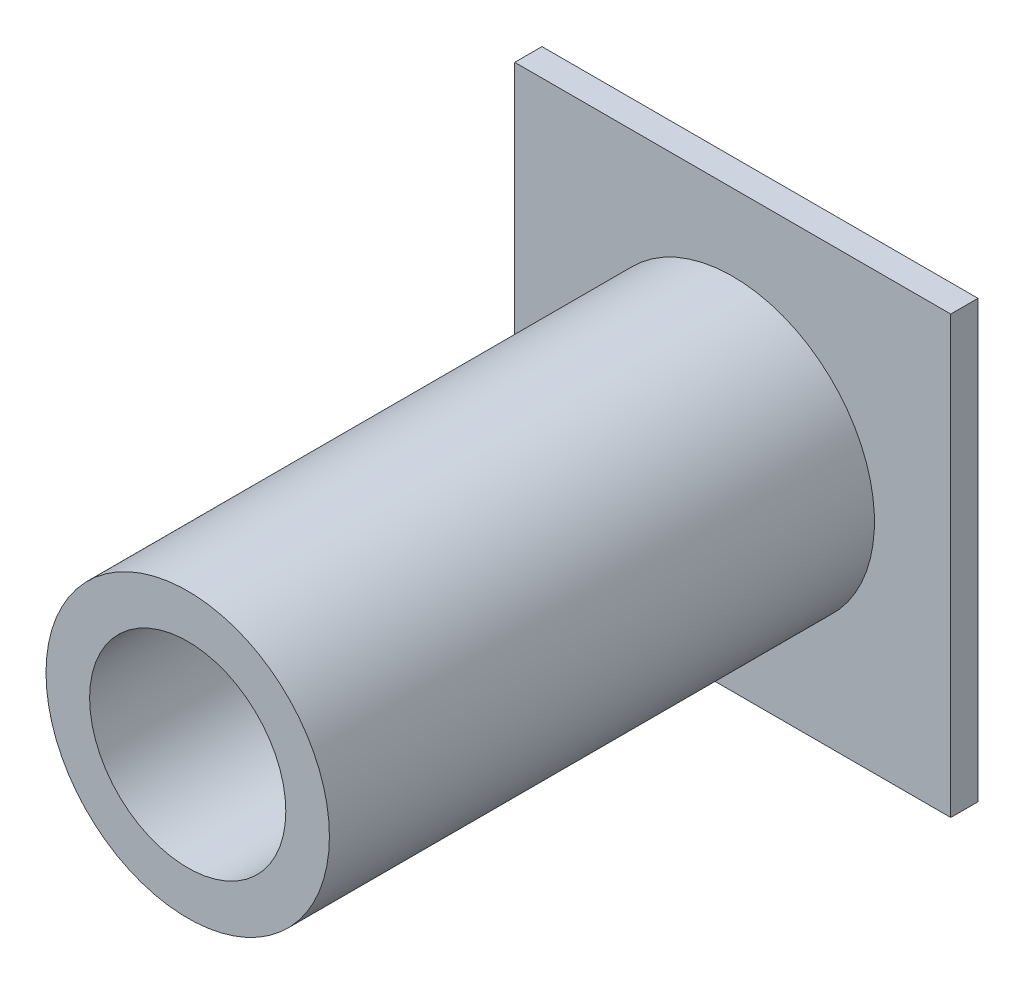
SolidWorks part; units mm, degrees
ref_plane "Front Plane" through (0, 0, 0) normal (0, 0, 1) x (1, 0, 0)
ref_plane "Top Plane" through (0, 0, 0) normal (0, 1, 0) x (1, 0, 0)
ref_plane "Right Plane" through (0, 0, 0) normal (1, 0, 0) x (0, 0, -1)
sketch "Sketch1" plane through (0, 0, 0) normal (0, 0, 1) x (1, 0, 0)
  line L1 (4, 4) -> (-4, 4)
  line L2 (4, 4) -> (4, -4)
  line L3 (4, -4) -> (-4, -4)
  line L4 (-4, 4) -> (-4, -4)
  dimension "D1" = 4
  dimension "D2" = 4
  dimension "D3" = 4
  dimension "D4" = 4
extrude "Boss-Extrude1" add sketch "Sketch1" along normal blind 0.5
sketch "Sketch4" plane through (0, 0, 0.5) normal (0, 0, 1) x (1, 0, 0)
  circle A0 centre (0, 0) radius 2.6
  dimension "D1" = 5.2
extrude "Boss-Extrude3" add sketch "Sketch4" along normal blind 10
sketch "Sketch6" plane through (0, 0, 10.5) normal (0, 0, 1) x (1, 0, 0)
  circle A0 centre (0, 0) radius 1.8
  dimension "D1" = 3.6
extrude "Cut-Extrude2" cut sketch "Sketch6" against normal up to surface (10 mm away) contours A0 up to face at (0, 0, 0.5)
